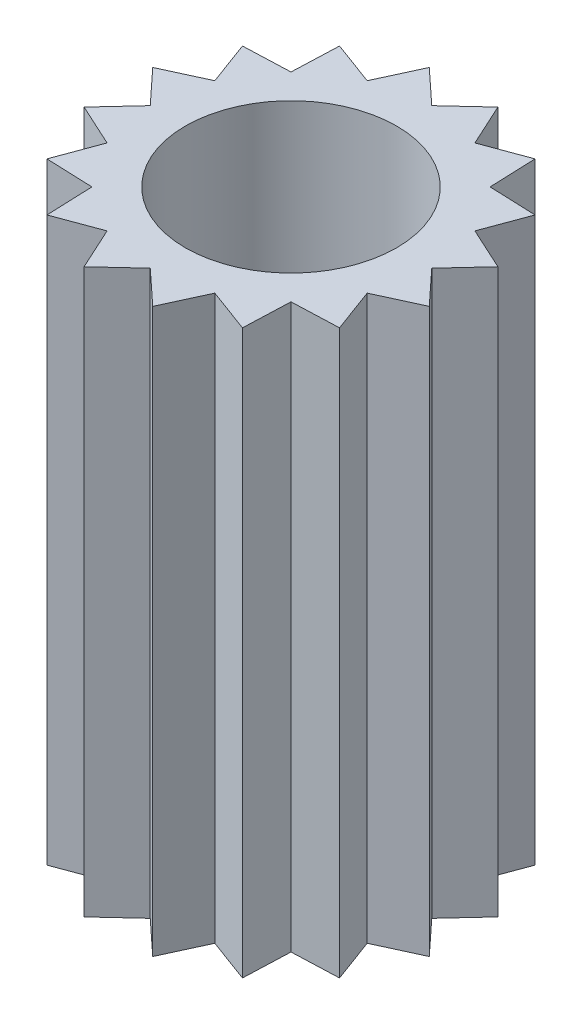
SolidWorks part; units mm, degrees
ref_plane "Front Plane" through (0, 0, 0) normal (0, 0, 1) x (1, 0, 0)
ref_plane "Top Plane" through (0, 0, 0) normal (0, 1, 0) x (1, 0, 0)
ref_plane "Right Plane" through (0, 0, 0) normal (1, 0, 0) x (0, 0, -1)
sketch "Sketch1" plane through (0, 0, 0) normal (0, 1, 0) x (1, 0, 0)
  line L0 (-2.5, 0) -> (2.5, 0) construction
  line L1 (0, 2.5) -> (0, -2.5) construction
  line L2 (1.7678, 1.7678) -> (-1.7678, -1.7678) construction
  line L3 (0.9567, 2.3097) -> (0, 0) construction
  line L4 (0, 2) -> (0.4877, 2.452)
  line L5 (0.4877, 2.452) -> (0.7654, 1.8478)
  line L6 (0, 0) -> (0.4877, 2.452) construction
  line L7 (0.7654, 1.8478) -> (1.3889, 2.0787)
  line L8 (1.3889, 2.0787) -> (1.4142, 1.4142)
  line L9 (1.4142, 1.4142) -> (2.0787, 1.3889)
  line L10 (2.0787, 1.3889) -> (1.8478, 0.7654)
  line L11 (1.8478, 0.7654) -> (2.452, 0.4877)
  line L12 (2.452, 0.4877) -> (2, 0)
  line L13 (2, 0) -> (2.452, -0.4877)
  line L14 (2.452, -0.4877) -> (1.8478, -0.7654)
  line L15 (1.8478, -0.7654) -> (2.0787, -1.3889)
  line L16 (2.0787, -1.3889) -> (1.4142, -1.4142)
  line L17 (1.4142, -1.4142) -> (1.3889, -2.0787)
  line L18 (1.3889, -2.0787) -> (0.7654, -1.8478)
  line L19 (0.7654, -1.8478) -> (0.4877, -2.452)
  line L20 (0.4877, -2.452) -> (0, -2)
  line L21 (0, -2) -> (-0.4877, -2.452)
  line L22 (-0.4877, -2.452) -> (-0.7654, -1.8478)
  line L23 (-0.7654, -1.8478) -> (-1.3889, -2.0787)
  line L24 (-1.3889, -2.0787) -> (-1.4142, -1.4142)
  line L25 (-1.4142, -1.4142) -> (-2.0787, -1.3889)
  line L26 (-2.0787, -1.3889) -> (-1.8478, -0.7654)
  line L27 (-1.8478, -0.7654) -> (-2.452, -0.4877)
  line L28 (-2.452, -0.4877) -> (-2, 0)
  line L29 (-2, 0) -> (-2.452, 0.4877)
  line L30 (-2.452, 0.4877) -> (-1.8478, 0.7654)
  line L31 (-1.8478, 0.7654) -> (-2.0787, 1.3889)
  line L32 (-2.0787, 1.3889) -> (-1.4142, 1.4142)
  line L33 (-1.4142, 1.4142) -> (-1.3889, 2.0787)
  line L34 (-1.3889, 2.0787) -> (-0.7654, 1.8478)
  line L35 (-0.7654, 1.8478) -> (-0.4877, 2.452)
  line L36 (-0.4877, 2.452) -> (0, 2)
  circle A0 centre (0, 0) radius 1.5
  circle A1 centre (0, 0) radius 2.5 construction
  circle A2 centre (0, 0) radius 2 construction
  point P64 (0, 0)
  dimension "D1" = 3
  dimension "D2" = 5
  dimension "D3" = 4
  dimension "D4" = 45
  dimension "D5" = 22.5
  dimension "D6" = 11.25
  dimension "D7" = 16
extrude "Boss-Extrude1" add sketch "Sketch1" along normal blind 8
